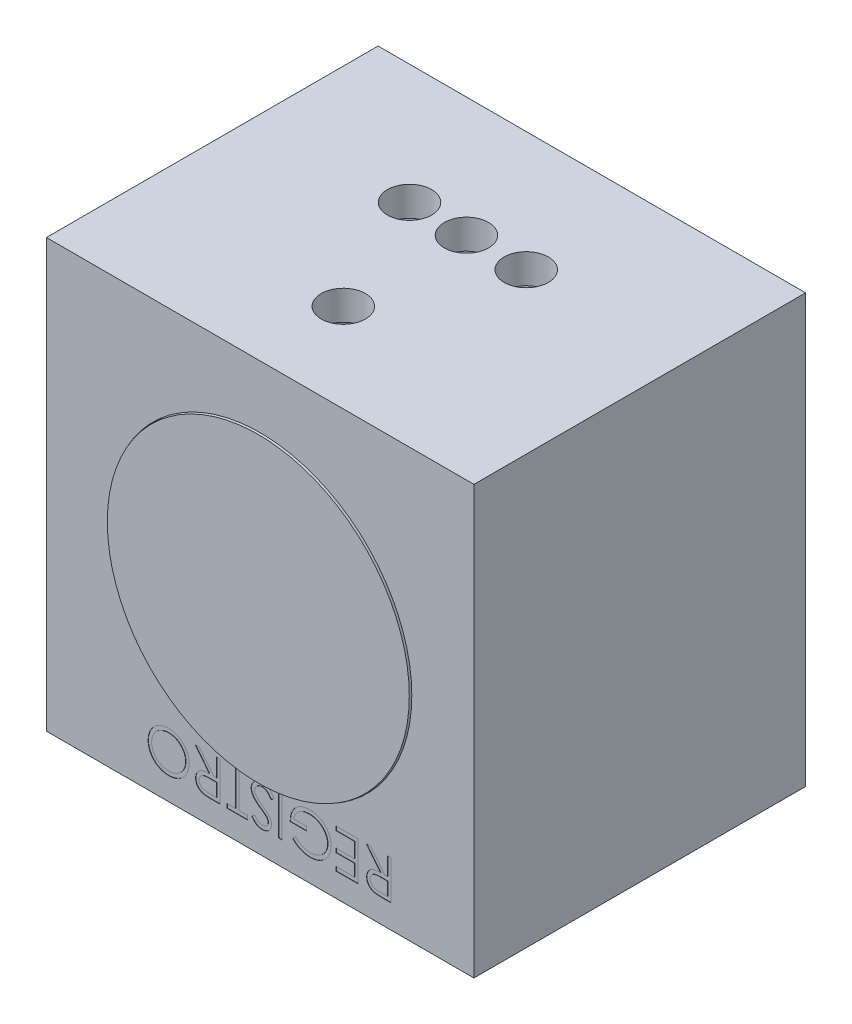
SolidWorks part; units mm, degrees
ref_plane "Alzado" through (0, 0, 0) normal (0, 0, 1) x (1, 0, 0)
ref_plane "Planta" through (0, 0, 0) normal (0, 1, 0) x (1, 0, 0)
ref_plane "Vista lateral" through (0, 0, 0) normal (1, 0, 0) x (0, 0, -1)
sketch "Croquis1" plane through (0, 0, 0) normal (0, 0, 1) x (1, 0, 0)
  line L0 (-330, 330) -> (-330, -670)
  line L1 (-410, -750) -> (750, -750)
  line L2 (-410, -750) -> (-410, 410)
  line L3 (-410, 410) -> (750, 410)
  line L4 (750, -750) -> (750, 410)
  line L5 (-330, 330) -> (670, 330)
  line L6 (670, 330) -> (670, -670)
  line L7 (670, -670) -> (-330, -670)
  point P0 (0, 0)
  dimension "D1" = 1160
  dimension "D2" = 1160
  dimension "D3" = 80
  dimension "D4" = 80
  dimension "D5" = 80
  dimension "D6" = 80
extrude "Saliente-Extruir2" add sketch "Croquis1" along normal blind 900
sketch "Croquis2" plane through (0, 0, 0) normal (0, 0, -1) x (-1, 0, 0)
  line L0 (-750, 410) -> (410, 410)
  line L1 (410, 410) -> (410, -750)
  line L2 (410, -750) -> (-750, -750)
  line L3 (-750, -750) -> (-750, 410)
extrude "Saliente-Extruir3" add sketch "Croquis2" against normal blind 80
sketch "Croquis3" plane through (0, 0, 0) normal (0, 0, -1) x (-1, 0, 0)
  line L1 (-750, -750) -> (-750, 410) construction
  line L2 (-150, 150) -> (-190, 150)
  line L3 (-150, -150) -> (-190, -150)
  line L4 (410, -750) -> (-750, -750) construction
  line L5 (-150, 150) -> (-150, -150)
  line L7 (-190, 150) -> (-190, -150)
  line L8 (410, 410) -> (410, -750) construction
  dimension "D2" = 600
  dimension "D3" = 600
  dimension "D4" = 600
sketch "Croquis5" plane through (0, -750, 0) normal (0, -1, 0) x (1, 0, 0)
  circle A0 centre (154.4068, 324.6899) radius 60
  circle A1 centre (0, 324.6899) radius 60
  circle A2 centre (316.6382, 324.6899) radius 60
  circle A3 centre (154.4068, 658.7445) radius 60
  dimension "D11" = 120
  dimension "D12" = 120
  dimension "D13" = 120
  dimension "D14" = 120
extrude "Cortar-Extruir2" cut sketch "Croquis5" against normal up to surface (1160 mm away) up to face at (170, 410, 450)
sketch "Croquis7" plane through (0, 0, 900) normal (0, 0, 1) x (1, 0, 0)
  line L1 (750, -750) -> (-410, -750)
  line L2 (750, -750) -> (750, 410)
  line L3 (750, 410) -> (-410, 410)
  line L4 (-410, -750) -> (-410, 410)
  line L5 (750, -750) -> (-410, 410) construction
  line L6 (750, 410) -> (-410, -750) construction
  circle A0 centre (170, -170) radius 387.5
  point P0 (170, -170)
  dimension "D1" = 775
extrude "Saliente-Extruir5" add sketch "Croquis7" against normal blind 100
sketch "Croquis8" plane through (0, 0, 900) normal (0, 0, 1) x (1, 0, 0)
  line L0 (597.5077, -580.0907) -> (-201.8881, -580.0907) construction
  text T0 "REGISTRO" font "Century Gothic" height in points 400
extrude "Cortar-Extruir3" cut sketch "Croquis8" against normal blind 1
sketch "Croquis9" plane through (0, 0, 900) normal (0, 0, 1) x (1, 0, 0)
  line L0 (557.5, -170) -> (170, -170) construction
  line L1 (170, -170) -> (170, -557.5) construction
  circle A0 centre (170, -170) radius 387.5 construction
  circle A1 centre (170, -170) radius 387.5 construction
  circle A2 centre (170, -170) radius 411.5
  circle A3 centre (170, -170) radius 387.5
  dimension "D1" = 823
extrude "Cortar-Extruir4" cut sketch "Croquis9" against normal blind 75
sketch "Croquis10" plane through (0, 0, 900) normal (0, 0, 1) x (1, 0, 0)
  circle A0 centre (170, -170) radius 409.6686
extrude "Saliente-Extruir6" add sketch "Croquis10" against normal blind 75 and the other way blind 5
sketch "Croquis11" plane through (0, 0, 0) normal (0, 0, -1) x (-1, 0, 0)
  line L0 (-750, -170) -> (410, -170) construction
  line L1 (-750, -750) -> (-750, 410) construction
  line L2 (410, 410) -> (410, -750) construction
  line L3 (410, -170) -> (-170, -170) construction
  line L4 (-170, -170) -> (-170, 410) construction
  line L5 (-750, 410) -> (410, 410) construction
  line L7 (-320, -20) -> (-20, -20)
  line L8 (-320, -20) -> (-320, -320)
  line L9 (-320, -320) -> (-20, -320)
  line L10 (-20, -20) -> (-20, -320)
  line L11 (-320, -20) -> (-20, -320) construction
  line L12 (-320, -320) -> (-20, -20) construction
  dimension "D1" = 300
  dimension "D2" = 300
extrude "Cortar-Extruir5" cut sketch "Croquis11" against normal blind 153
